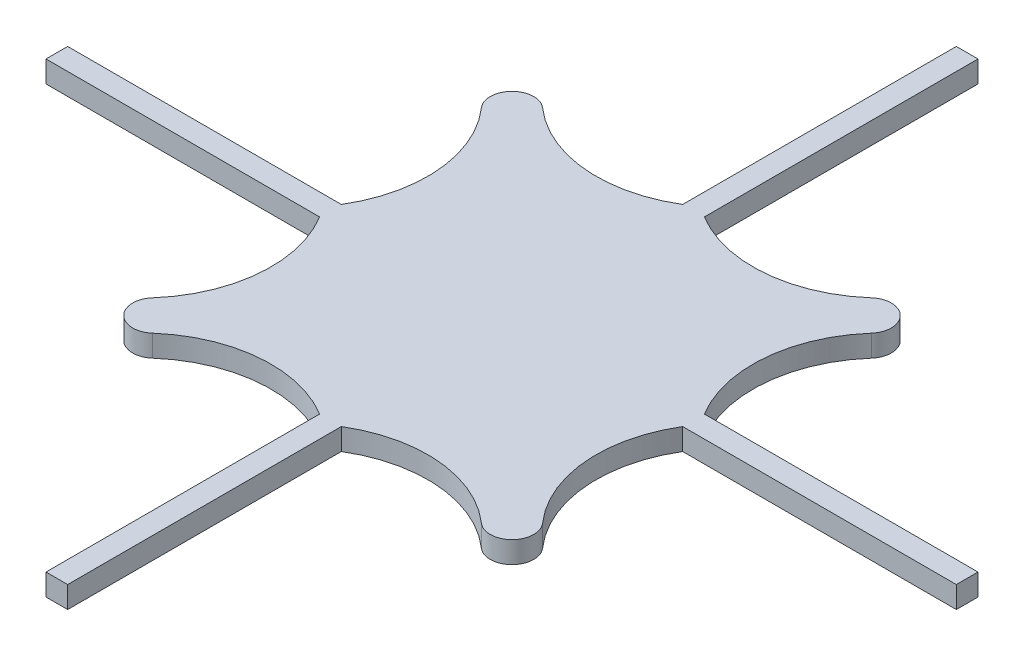
SolidWorks part; units mm, degrees
ref_plane "Front Plane" through (0, 0, 0) normal (0, 0, 1) x (1, 0, 0)
ref_plane "Top Plane" through (0, 0, 0) normal (0, 1, 0) x (1, 0, 0)
ref_plane "Right Plane" through (0, 0, 0) normal (1, 0, 0) x (0, 0, -1)
sketch "Sketch1" plane through (0, 0, 0) normal (0, 1, 0) x (1, 0, 0)
  line L0 (-23.2691, -2.2463) -> (-41.1833, 15.6679) construction
  line L1 (-38.2691, 12.7537) -> (-8.2691, 12.7537) construction
  line L2 (-65.2691, -1.2463) -> (-65.2691, -3.2463)
  line L3 (-65.2691, -1.2463) -> (-40.019, -1.2463)
  line L4 (18.7309, -1.2463) -> (18.7309, -3.2463)
  line L5 (-23.2691, 39.7537) -> (-23.2691, -17.2463) construction
  line L6 (-38.2691, -2.2463) -> (-8.2691, -2.2463) construction
  line L8 (18.7309, -1.2463) -> (-6.5192, -1.2463)
  line L9 (-24.2691, 39.7537) -> (-24.2691, 14.5037)
  line L10 (-22.2691, 39.7537) -> (-22.2691, 14.5037)
  line L11 (-65.2691, -3.2463) -> (-40.019, -3.2463)
  line L12 (-24.2691, -44.2463) -> (-24.2691, -18.9962)
  line L13 (-24.2691, -44.2463) -> (-22.2691, -44.2463)
  line L14 (-22.2691, -44.2463) -> (-22.2691, -18.9962)
  line L15 (-24.2691, 39.7537) -> (-22.2691, 39.7537)
  line L16 (18.7309, -3.2463) -> (-6.5192, -3.2463)
  arc A0 (-41.2691, 12.9309) -> (-40.019, -1.2463) centre (-50.2691, 4.9936) cw
  arc A1 (-5.2691, 12.9309) -> (-6.5192, -1.2463) centre (3.7309, 4.9936) ccw
  arc A2 (-8.092, 15.7537) -> (-5.2691, 12.9309) centre (-6.7691, 14.2537) cw
  arc A3 (-8.092, 15.7537) -> (-22.2691, 14.5037) centre (-16.0292, 24.7537) cw
  arc A4 (-41.2691, -17.4234) -> (-40.019, -3.2463) centre (-50.2691, -9.4861) ccw
  arc A5 (-38.4462, 15.7537) -> (-24.2691, 14.5037) centre (-30.509, 24.7537) ccw
  arc A6 (-38.4462, -20.2463) -> (-41.2691, -17.4234) centre (-39.7691, -18.7463) cw
  arc A7 (-38.4462, -20.2463) -> (-24.2691, -18.9962) centre (-30.509, -29.2463) cw
  arc A8 (-8.092, -20.2463) -> (-22.2691, -18.9962) centre (-16.0292, -29.2463) ccw
  arc A9 (-8.092, -20.2463) -> (-5.2691, -17.4234) centre (-6.7691, -18.7463) ccw
  arc A10 (-5.2691, -17.4234) -> (-6.5192, -3.2463) centre (3.7309, -9.4861) cw
  arc A11 (-38.4462, 15.7537) -> (-41.2691, 12.9309) centre (-39.7691, 14.2537) ccw
  point P28 (-65.2691, -2.2463)
  point P46 (18.7309, -2.2463)
  dimension "D6" = 27
  dimension "D4" = 12
  dimension "D5" = 15
  dimension "D3" = 16.5
  dimension "D1" = 2
  dimension "D8" = 1
extrude "Boss-Extrude1" add sketch "Sketch1" along normal blind 2
